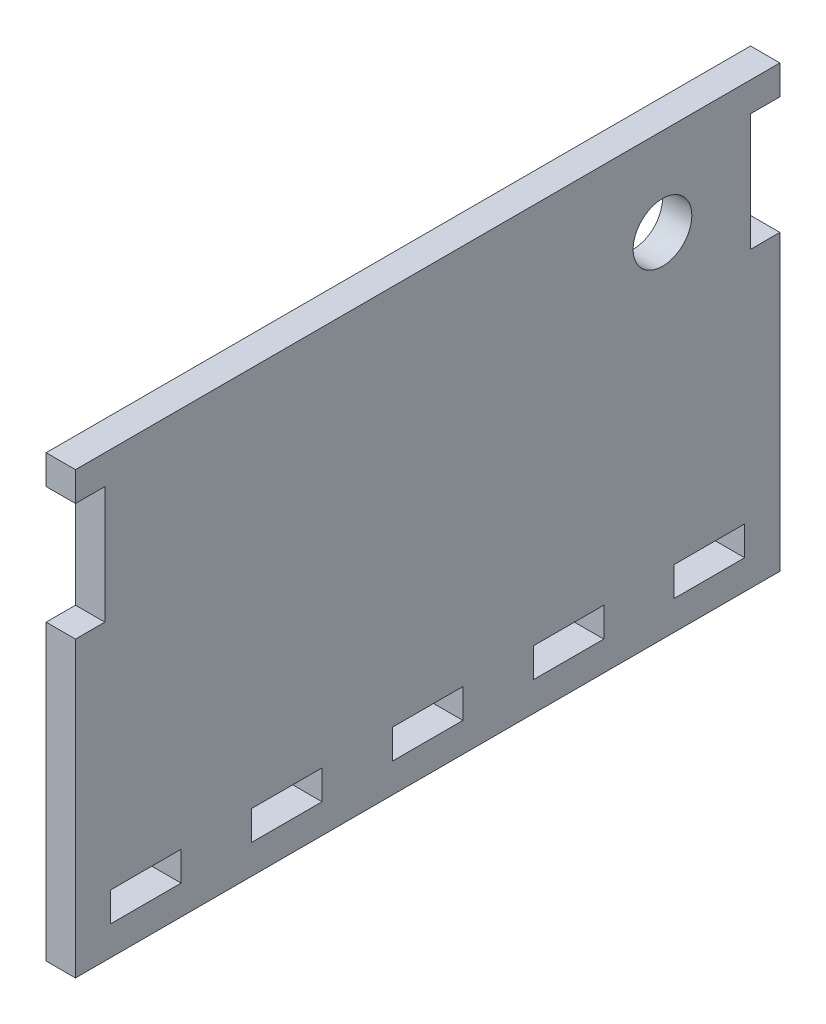
SolidWorks part; units mm, degrees
ref_plane "Front Plane" through (0, 0, 0) normal (0, 0, 1) x (1, 0, 0)
ref_plane "Top Plane" through (0, 0, 0) normal (0, 1, 0) x (1, 0, 0)
ref_plane "Right Plane" through (0, 0, 0) normal (1, 0, 0) x (0, 0, -1)
sketch "Sketch1" plane through (0, 0, 0) normal (1, 0, 0) x (0, 0, -1)
  line L0 (-19.05, -17.4625) -> (-19.05, -20.6375)
  line L1 (-38.1, -23.8125) -> (38.1, -23.8125)
  line L2 (-38.1, -23.8125) -> (-38.1, 7.9375)
  line L3 (-38.1, 23.8125) -> (38.1, 23.8125)
  line L4 (38.1, -23.8125) -> (38.1, 7.9375)
  line L5 (-38.1, -23.8125) -> (38.1, 23.8125) construction
  line L6 (-38.1, 23.8125) -> (38.1, -23.8125) construction
  line L7 (-38.1, 20.6375) -> (-34.925, 20.6375)
  line L9 (-38.1, 7.9375) -> (-34.925, 7.9375)
  line L10 (-34.925, 20.6375) -> (-34.925, 7.9375)
  line L11 (38.1, 20.6375) -> (34.925, 20.6375)
  line L13 (38.1, 7.9375) -> (34.925, 7.9375)
  line L14 (34.925, 20.6375) -> (34.925, 7.9375)
  line L15 (-34.29, -17.4625) -> (-26.67, -17.4625)
  line L16 (-34.29, -17.4625) -> (-34.29, -20.6375)
  line L17 (-34.29, -20.6375) -> (-26.67, -20.6375)
  line L18 (-26.67, -17.4625) -> (-26.67, -20.6375)
  line L19 (-19.05, -17.4625) -> (-11.43, -17.4625)
  line L20 (-11.43, -17.4625) -> (-11.43, -20.6375)
  line L21 (-19.05, -20.6375) -> (-11.43, -20.6375)
  line L22 (-3.81, -17.4625) -> (-3.81, -20.6375)
  line L23 (-3.81, -17.4625) -> (3.81, -17.4625)
  line L24 (3.81, -17.4625) -> (3.81, -20.6375)
  line L25 (-3.81, -20.6375) -> (3.81, -20.6375)
  line L26 (11.43, -17.4625) -> (11.43, -20.6375)
  line L27 (11.43, -17.4625) -> (19.05, -17.4625)
  line L28 (19.05, -17.4625) -> (19.05, -20.6375)
  line L29 (11.43, -20.6375) -> (19.05, -20.6375)
  line L30 (26.67, -17.4625) -> (26.67, -20.6375)
  line L31 (26.67, -17.4625) -> (34.29, -17.4625)
  line L32 (34.29, -17.4625) -> (34.29, -20.6375)
  line L33 (26.67, -20.6375) -> (34.29, -20.6375)
  line L34 (-38.1, 20.6375) -> (-38.1, 23.8125)
  line L35 (38.1, 20.6375) -> (38.1, 23.8125)
  circle A0 centre (25.4, 14.2875) radius 3.175
  point P0 (0, 0)
  dimension "D14" = 6.35
  dimension "D1" = 47.625
  dimension "D2" = 76.2
  dimension "D3" = 3.175
  dimension "D4" = 12.7
  dimension "D5" = 3.175
  dimension "D6" = 3.175
  dimension "D7" = 12.7
  dimension "D8" = 3.175
  dimension "D9" = 3.175
  dimension "D10" = 7.62
  dimension "D11" = 3.81
  dimension "D12" = 3.175
  dimension "D15" = 9.525
  dimension "D16" = 12.7
  dimension "D13" = 5
extrude "Boss-Extrude1" add sketch "Sketch1" along normal mid plane 3.175
